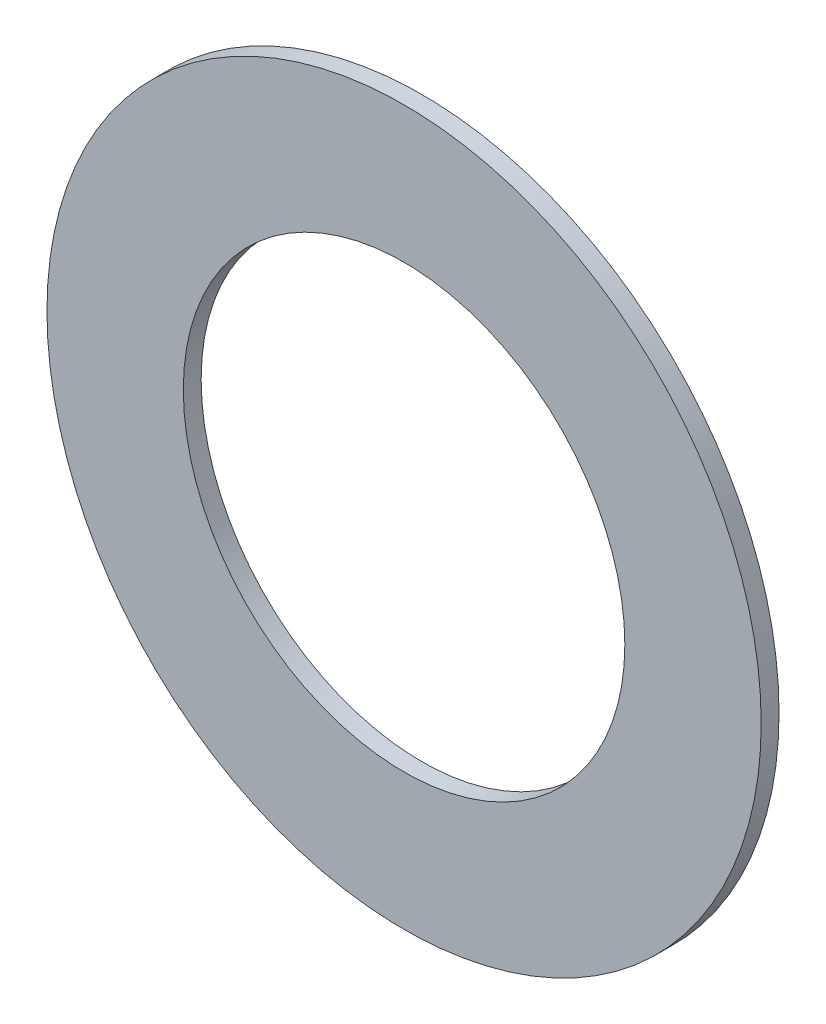
SolidWorks part; units mm, degrees
ref_plane "Front Plane" through (0, 0, 0) normal (0, 0, 1) x (1, 0, 0)
ref_plane "Top Plane" through (0, 0, 0) normal (0, 1, 0) x (1, 0, 0)
ref_plane "Right Plane" through (0, 0, 0) normal (1, 0, 0) x (0, 0, -1)
sketch "Sketch1" plane through (0, 0, 0) normal (0, 0, 1) x (1, 0, 0)
  circle A0 centre (0, 0) radius 63.5
  circle A1 centre (0, 0) radius 39.2557
  dimension "D1" = 78.5114
  dimension "D2" = 127
extrude "Boss-Extrude1" add sketch "Sketch1" along normal blind 3.175
equation "\"AIRFRAME_OD\"= 5.15in"
equation "\"AIRFRAME_ID\"= 5.00in"
equation "\"FLAT_T\"= 0.125in"
equation "\"COUPLER_OD\"= 4.998in"
equation "\"COUPLER_ID\"= 4.88in"
equation "\"NOSE_EXP_L\"= 27in"
equation "\"NOSE_SHOULDER_L\"= 5in"
equation "\"MAIN_L\"= 30in"
equation "\"RECO_COUP_L\"= 10in"
equation "\"RECO_SWITCH_L\"= 2in"
equation "\"RECO_ROD_X\"= 3.5in"
equation "\"DROGUE_L\"= 20in"
equation "\"ATS_FORE_COUP_L\"= 5.5in"
equation "\"ATS_AFT_COUP_L\"= 4.5in"
equation "\"ATS_ROD_X\"= 3.75in"
equation "\"LOWER_L\"= 30in"
equation "\"FIN_ROOT\"= 8in"
equation "\"FIN_X\"= 0.75in"
equation "\"FIN_N\"= 4"
equation "\"MOTOR_OD\"= 3.091in"
equation "\"MOTOR_ID\"= 3.00in"
equation "\"MOTOR_L\"= 14in"
equation "\"CR_AFT_X\"= 0.5in"
equation "\"CR_FORE_X\"= 9.25in"
equation "\"D1@Boss-Extrude1\"=\"FLAT_T\""
equation "\"D1@Sketch1\"=\"MOTOR_OD\""
equation "\"D2@Sketch1\"=\"AIRFRAME_ID\""
equation "\"MOTOR_LOWER_X\"= 2in"
